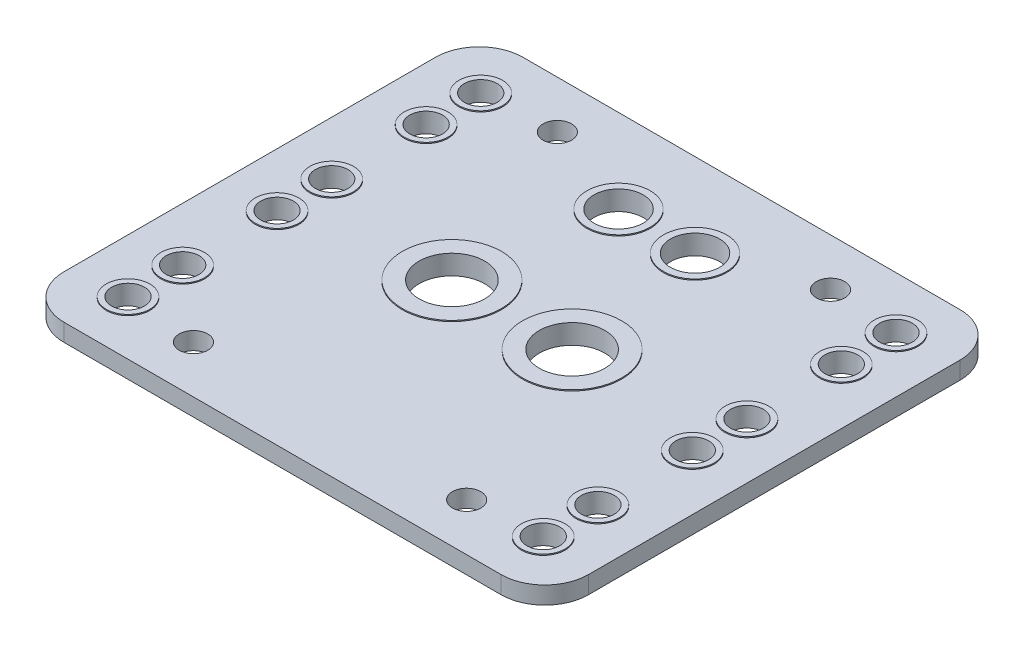
SolidWorks part; units mm, degrees
ref_plane "Alzado" through (0, 0, 0) normal (0, 0, 1) x (1, 0, 0)
ref_plane "Planta" through (0, 0, 0) normal (0, 1, 0) x (1, 0, 0)
ref_plane "Vista lateral" through (0, 0, 0) normal (1, 0, 0) x (0, 0, -1)
sketch "Croquis1" plane through (0, 0, 0) normal (0, 1, 0) x (1, 0, 0)
  line L1 (-20, 21) -> (20, 21)
  line L2 (-24, 17) -> (-24, -17)
  line L3 (-20, -21) -> (20, -21)
  line L4 (24, 17) -> (24, -17)
  line L5 (-24, 21) -> (24, -21) construction
  line L6 (-24, -21) -> (24, 21) construction
  arc A0 (20, 21) -> (24, 17) centre (20, 17) cw
  arc A1 (20, -21) -> (24, -17) centre (20, -17) ccw
  arc A2 (-24, -17) -> (-20, -21) centre (-20, -17) ccw
  arc A3 (-20, 21) -> (-24, 17) centre (-20, 17) ccw
  point P0 (0, 0)
  dimension "D1" = 4
  dimension "D2" = 42
  dimension "D3" = 48
extrude "Saliente-Extruir1" add sketch "Croquis1" along normal mid plane 1.6
sketch "Croquis2" plane through (0, 0.8, 0) normal (0, 1, 0) x (1, 0, 0)
  line L1 (12.5, -16.65) -> (-12.5, -16.65) construction
  line L2 (12.5, -16.65) -> (12.5, 16.65) construction
  line L3 (12.5, 16.65) -> (-12.5, 16.65) construction
  line L4 (-12.5, -16.65) -> (-12.5, 16.65) construction
  line L5 (12.5, -16.65) -> (-12.5, 16.65) construction
  line L6 (12.5, 16.65) -> (-12.5, -16.65) construction
  circle A0 centre (-12.5, 16.65) radius 1.3
  circle A1 centre (12.5, 16.65) radius 1.3
  circle A2 centre (12.5, -16.65) radius 1.3
  circle A3 centre (-12.5, -16.65) radius 1.3
  point P0 (0, 0)
  dimension "D1" = 2.6
  dimension "D2" = 33.3
  dimension "D3" = 25
extrude "Cortar-Extruir1" cut sketch "Croquis2" against normal through all both and the other way through all
sketch "Croquis3" plane through (0, 0.8, 0) normal (0, 1, 0) x (1, 0, 0)
  line L0 (-5.5, 0) -> (5.5, 0) construction
  circle A0 centre (-5.5, 0) radius 3
  circle A1 centre (5.5, 0) radius 3
  point P4 (0, 0)
  dimension "D1" = 6
  dimension "D2" = 11
extrude "Cortar-Extruir2" cut sketch "Croquis3" against normal through all
sketch "Croquis5" plane through (0, 0, 0) normal (0, 1, 0) x (1, 0, 0)
  circle A0 centre (-5.5, 0) radius 3
  circle A1 centre (-5.5, 0) radius 4.5337
  circle A2 centre (5.5, 0) radius 3
  circle A3 centre (5.5, 0) radius 4.5337
  circle A4 centre (-5.5, 0) radius 3 construction
extrude "Saliente-Extruir2" add sketch "Croquis5" along normal mid plane 1.8
sketch "Croquis6" plane through (0, 0.8, 0) normal (0, 1, 0) x (1, 0, 0)
  line L0 (-3.5, 13.25) -> (3.5, 13.25) construction
  line L1 (0, 23.1314) -> (0, -25.294) construction
  line L2 (-19, 16.14) -> (-19, 11.14) construction
  line L3 (-19, 2.5) -> (-19, -2.5) construction
  line L4 (-19, -11.14) -> (-19, -16.14) construction
  line L5 (-24, 17) -> (-24, -17) construction
  line L6 (20, 21) -> (-20, 21) construction
  line L7 (-20, -21) -> (20, -21) construction
  circle A0 centre (-3.5, 13.25) radius 2.25
  circle A1 centre (3.5, 13.25) radius 2.25
  circle A2 centre (-19, 2.5) radius 1.5
  circle A3 centre (-19, -2.5) radius 1.5
  circle A4 centre (-19, 11.14) radius 1.5
  circle A5 centre (-19, 16.14) radius 1.5
  circle A6 centre (-19, -11.14) radius 1.5
  circle A7 centre (-19, -16.14) radius 1.5
  circle A8 centre (19, -16.14) radius 1.5
  circle A9 centre (19, -11.14) radius 1.5
  circle A10 centre (19, 16.14) radius 1.5
  circle A11 centre (19, 11.14) radius 1.5
  circle A12 centre (19, -2.5) radius 1.5
  circle A13 centre (19, 2.5) radius 1.5
  point P4 (0, 13.25)
  point P32 (-19, 0)
  dimension "D1" = 3
  dimension "D8" = 4.5
  dimension "D2" = 5
  dimension "D3" = 5
  dimension "D4" = 5
  dimension "D5" = 5
  dimension "D6" = 4.86
  dimension "D7" = 4.86
  dimension "D9" = 7
  dimension "D10" = 7.75
extrude "Cortar-Extruir3" cut sketch "Croquis6" against normal through all
sketch "Croquis7" plane through (0, 0, 0) normal (0, 1, 0) x (1, 0, 0)
  line L0 (0, 6.6749) -> (0, -3.6027) construction
  circle A0 centre (-19, -16.14) radius 1.5
  circle A1 centre (-19, -11.14) radius 1.5
  circle A2 centre (-19, -2.5) radius 1.5
  circle A3 centre (-19, 2.5) radius 1.5
  circle A4 centre (-19, 11.14) radius 1.5
  circle A5 centre (-19, 16.14) radius 1.5
  circle A6 centre (-19, 16.14) radius 1.5 construction
  circle A7 centre (-19, 16.14) radius 2
  circle A8 centre (-19, 11.14) radius 2
  circle A9 centre (-19, 2.5) radius 2
  circle A10 centre (-19, -2.5) radius 2
  circle A11 centre (-19, -16.14) radius 2
  circle A12 centre (-19, -11.14) radius 2
  circle A13 centre (-3.5, 13.25) radius 2.25
  circle A14 centre (-3.5, 13.25) radius 2.8949
  circle A15 centre (3.5, 13.25) radius 2.8949
  circle A16 centre (3.5, 13.25) radius 2.25
  circle A17 centre (19, -11.14) radius 2
  circle A18 centre (19, -16.14) radius 2
  circle A19 centre (19, -2.5) radius 2
  circle A20 centre (19, 2.5) radius 2
  circle A21 centre (19, 11.14) radius 2
  circle A22 centre (19, 16.14) radius 2
  circle A23 centre (19, 16.14) radius 1.5
  circle A24 centre (19, 11.14) radius 1.5
  circle A25 centre (19, 2.5) radius 1.5
  circle A26 centre (19, -2.5) radius 1.5
  circle A27 centre (19, -11.14) radius 1.5
  circle A28 centre (19, -16.14) radius 1.5
  dimension "D1" = 4
extrude "Saliente-Extruir3" add sketch "Croquis7" along normal mid plane 1.8
